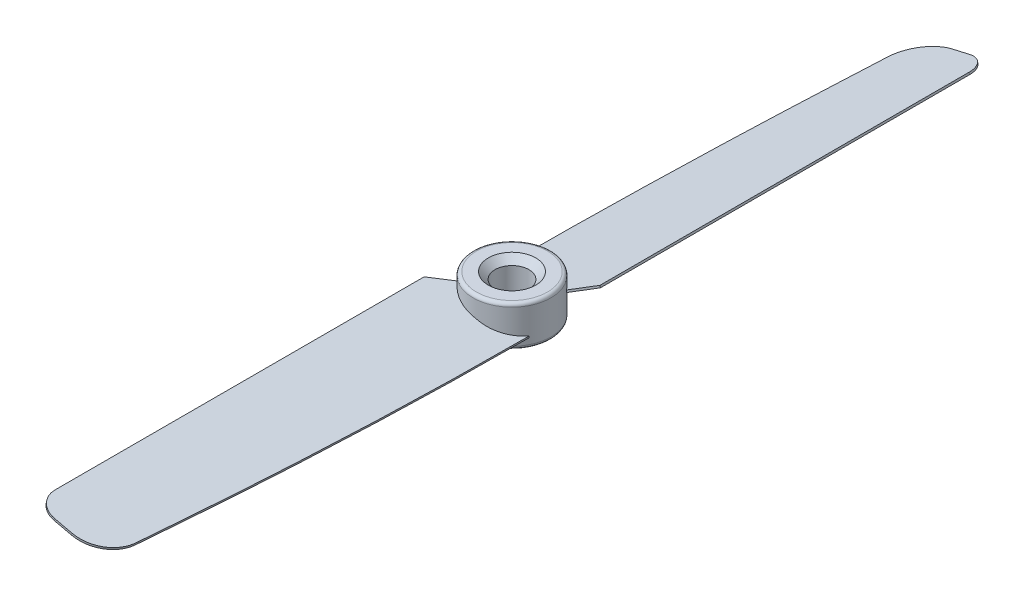
SolidWorks part; units mm, degrees
ref_plane "Front Plane" through (0, 0, 0) normal (0, 0, 1) x (1, 0, 0)
ref_plane "Top Plane" through (0, 0, 0) normal (0, 1, 0) x (1, 0, 0)
ref_plane "Right Plane" through (0, 0, 0) normal (1, 0, 0) x (0, 0, -1)
sketch "Sketch1" plane through (0, 0, 0) normal (0, 1, 0) x (1, 0, 0)
  circle A0 centre (0, 0) radius 5.75
  dimension "D1" = 11.5
extrude "Boss-Extrude1" add sketch "Sketch1" along normal mid plane 6
sketch "Sketch2" plane through (0, 0, 0) normal (0, 0, 1) x (1, 0, 0)
  line L0 (-5.75, 1.3275) -> (5.75, -1.3275) construction
  line L1 (-5.75, 3) -> (-5.75, -3) construction
  line L2 (5.75, -3) -> (5.75, 3) construction
  line L3 (-5.75, -3) -> (5.75, -3) construction
  dimension "D1" = 13
ref_plane "Plane1" through (0, 0, 0) normal (-0.225, -0.9744, 0) x (0.9744, -0.225, 0)
sketch "Sketch3" plane through (0, 0, 0) normal (-0.225, -0.9744, 0) x (0.9744, -0.225, 0)
  line L0 (-4.1784, 2.8728) -> (-7.26, 5.9545)
  line L1 (-7.26, 5.9545) -> (-7.26, 60.5)
  line L2 (-4.26, 63.5) -> (-1.6032, 63.5)
  arc A0 (3.3967, 58.5329) -> (-1.6032, 63.5) centre (-1.6032, 58.5) ccw
  arc A1 (-7.26, 60.5) -> (-4.26, 63.5) centre (-4.26, 60.5) cw
  ellipse E0 centre (0.6749, 0) end of major axis (0.6749, 5.75) minor radius 5.6026 construction
  ellipse E1 centre (0.6749, 0) end of major axis (0.6749, 5.75) minor radius 5.6026
  spline S0 degree 3 poles (5.5281, 2.8728) (5.4997, 33.8349) (3.407, 56.9678) (3.3967, 58.5329) knots 0 0 0 0 0.918194 0.918194 0.918194 0.918194
  dimension "D2" = 5
  dimension "D3" = 3
  dimension "D1" = 63.5
extrude "Boss-Extrude2" add sketch "Sketch3" along normal mid plane 0.3 contours E1 S0 A0 L2 A1 L1 L0
pattern_circular "CirPattern1" count 2 over 360 about axis through (0, 3, 0) along (0, -1, 0) of "Boss-Extrude2"
sketch "Sketch4" plane through (0, -3, 0) normal (0, -1, 0) x (1, 0, 0)
  circle A0 centre (0, 0) radius 2.5
  dimension "D1" = 5
extrude "Cut-Extrude1" cut sketch "Sketch4" against normal through all
fillet "Fillet1" radius 0.5 2 edges at (0, 3, 5.75) (0, -3, 5.75)
chamfer "Chamfer1" distance 1 angle 45 2 edges at (0, -3, -2.5) (0, 3, -2.5)
